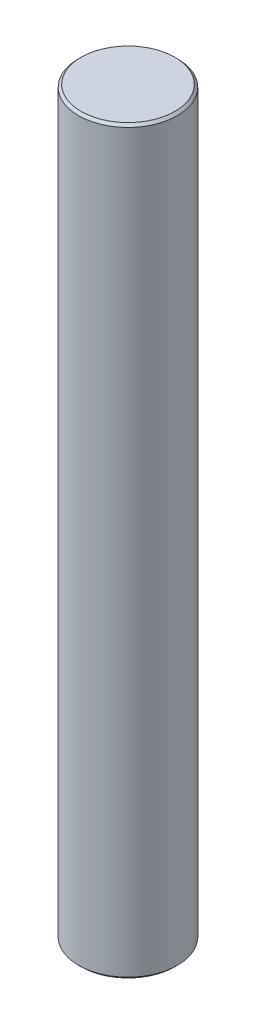
SolidWorks part; units mm, degrees
ref_plane "Front Plane" through (0, 0, 0) normal (0, 0, 1) x (1, 0, 0)
ref_plane "Top Plane" through (0, 0, 0) normal (0, 1, 0) x (1, 0, 0)
ref_plane "Right Plane" through (0, 0, 0) normal (1, 0, 0) x (0, 0, -1)
sketch "Sketch1" plane through (0, 0, 0) normal (0, 1, 0) x (1, 0, 0)
  circle A0 centre (0, 0) radius 2
  dimension "D1" = 4
extrude "Boss-Extrude1" add sketch "Sketch1" along normal blind 30
chamfer "Chamfer1" distance 0.1 angle 45 2 edges at (0, 0, 2) (0, 30, 2)
